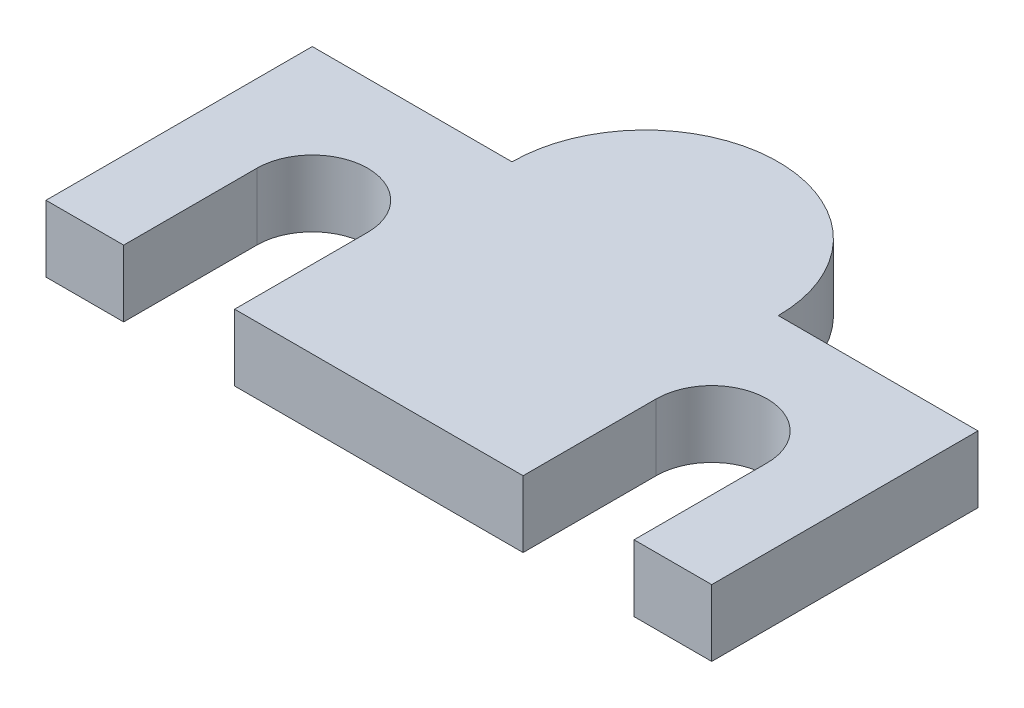
SolidWorks part; units mm, degrees
ref_plane "Front Plane" through (0, 0, 0) normal (0, 0, 1) x (1, 0, 0)
ref_plane "Top Plane" through (0, 0, 0) normal (0, 1, 0) x (1, 0, 0)
ref_plane "Right Plane" through (0, 0, 0) normal (1, 0, 0) x (0, 0, -1)
sketch "Sketch1" plane through (0, 0, 0) normal (0, 1, 0) x (1, 0, 0)
  line L1 (15, 6) -> (-15, 6)
  line L2 (15, 6) -> (15, -6)
  line L3 (15, -6) -> (-15, -6)
  line L4 (-15, 6) -> (-15, -6)
  line L5 (0, -6) -> (0, 6) construction
  line L6 (15, 0) -> (-15, 0) construction
  point P0 (0, 0)
  dimension "D1" = 30
  dimension "D2" = 12
extrude "Boss-Extrude1" add sketch "Sketch1" along normal blind 3
sketch "Sketch2" plane through (0, 3, 0) normal (0, 1, 0) x (1, 0, 0)
  line L0 (9, 0) -> (-9, 0) construction
  circle A0 centre (-9, 0) radius 1.5
  circle A1 centre (9, 0) radius 1.5
  point P4 (0, 0)
  dimension "D1" = 3
  dimension "D2" = 18
extrude "Cut-Extrude1" cut sketch "Sketch2" against normal through all
sketch "Sketch3" plane through (0, 3, 0) normal (0, 1, 0) x (1, 0, 0)
  line L0 (-9, 0) -> (-9, -6) construction
  line L1 (-15, -6) -> (15, -6) construction
  line L2 (-6.5, 0) -> (-6.5, -6)
  line L3 (-11.5, 0) -> (-11.5, -6)
  line L4 (9, 0) -> (9, -6) construction
  line L5 (11.5, 0) -> (11.5, -6)
  line L6 (6.5, 0) -> (6.5, -6)
  arc A0 (-6.5, 0) -> (-11.5, 0) centre (-9, 0) ccw
  arc A1 (-11.5, -6) -> (-6.5, -6) centre (-9, -6) ccw
  arc A2 (11.5, 0) -> (6.5, 0) centre (9, 0) ccw
  arc A3 (6.5, -6) -> (11.5, -6) centre (9, -6) ccw
  point P5 (-9, -3)
  point P10 (9, -3)
  dimension "D1" = 5
  dimension "D2" = 6
extrude "Cut-Extrude2" cut sketch "Sketch3" against normal through all
sketch "Sketch4" plane through (0, 0, 0) normal (0, -1, 0) x (1, 0, 0)
  line L0 (0, -6) -> (0, 0) construction
  line L1 (15, -6) -> (-15, -6) construction
  line L2 (-6, -6) -> (-6, 0)
  line L3 (6, -6) -> (6, 0)
  arc A0 (-6, -6) -> (6, -6) centre (0, -6) ccw
  arc A1 (6, 0) -> (-6, 0) centre (0, 0) ccw
  point P5 (0, -3)
  dimension "D1" = 12
  dimension "D2" = 6
extrude "Boss-Extrude2" add sketch "Sketch4" against normal blind 3
